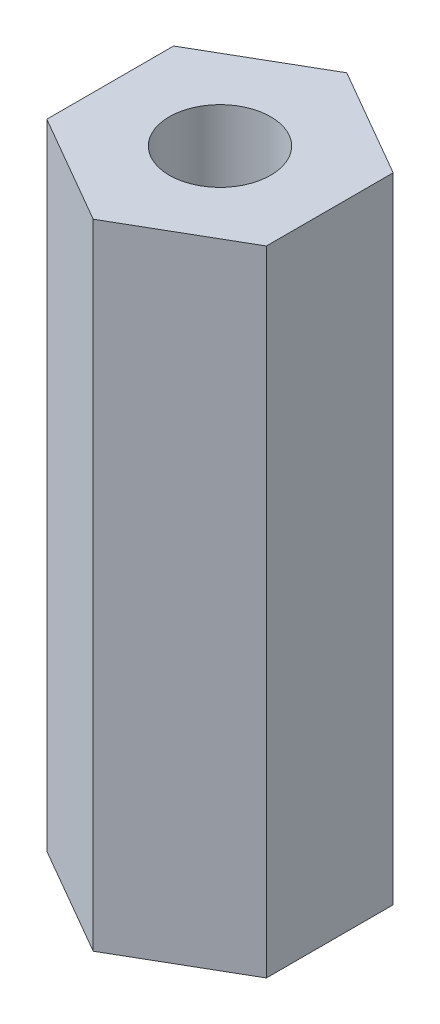
SolidWorks part; units mm, degrees
ref_plane "Front Plane" through (0, 0, 0) normal (0, 0, 1) x (1, 0, 0)
ref_plane "Top Plane" through (0, 0, 0) normal (0, 1, 0) x (1, 0, 0)
ref_plane "Right Plane" through (0, 0, 0) normal (1, 0, 0) x (0, 0, -1)
sketch "Sketch1" plane through (0, 0, 0) normal (0, 1, 0) x (1, 0, 0)
  line L1 (1.7321, -1) -> (1.7321, 1)
  line L2 (1.7321, 1) -> (0, 2)
  line L3 (0, 2) -> (-1.7321, 1)
  line L4 (-1.7321, 1) -> (-1.7321, -1)
  line L5 (-1.7321, -1) -> (0, -2)
  line L6 (0, -2) -> (1.7321, -1)
  circle A0 centre (0, 0) radius 1.7321 construction
  dimension "D1" = 2
  dimension "D2" = 2
extrude "Boss-Extrude1" add sketch "Sketch1" along normal blind 10
hole_wizard "M2x0.4 Tapped Hole1" positions "Sketch3" profile "Sketch2" tap size "M2x0.4" standard "ANSI Metric" end condition through all
sketch "Sketch3" plane through (0, 10, 0) normal (0, 1, 0) x (1, 0, 0)
  point P0 (0, 0)
sketch "Sketch2" plane through (0, 10, 0) normal (1, 0, 0) x (0, 0, 1)
  line L0 (0, 0) -> (0, 10)
  line L1 (0, 10) -> (0.8, 10)
  line L2 (0.8, 10) -> (0.8, 0)
  line L5 (0.8, 0) -> (0, 0)
  line L11 (0, -6.35) -> (0, 107.95) construction
  dimension "Thru Tap Drill Dia." = 1.6
  dimension "Thru Tap Drill Depth" = 10
cosmetic thread "Hole Thread1"
